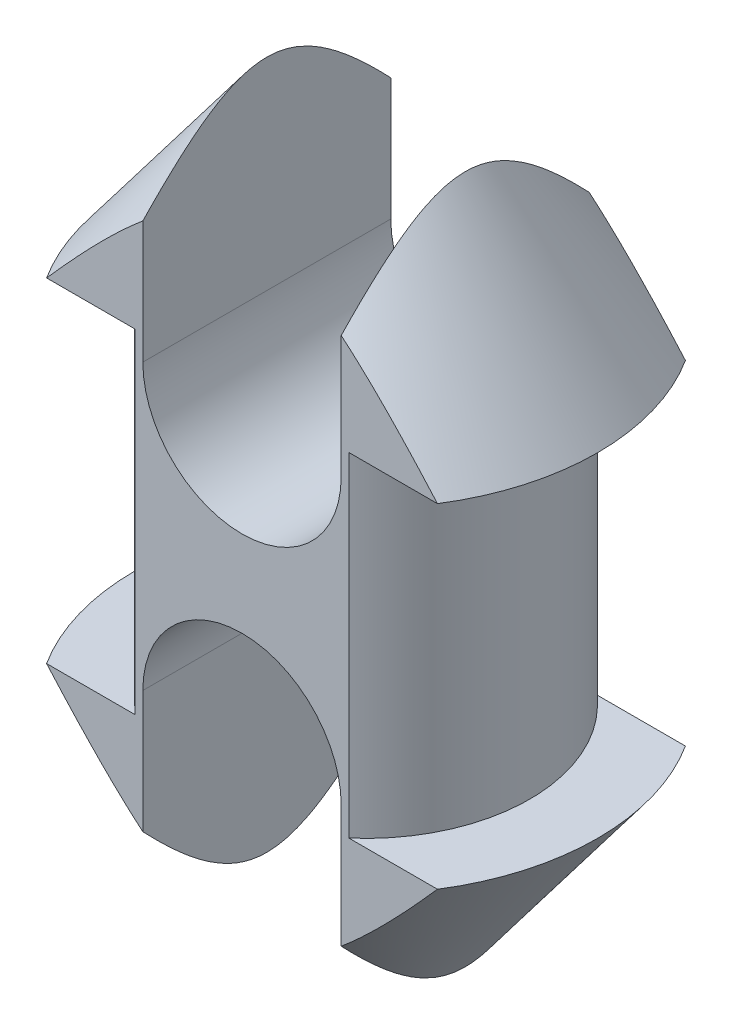
SolidWorks part; units mm, degrees
ref_plane "Plano frontal" through (0, 0, 0) normal (0, 0, 1) x (1, 0, 0)
ref_plane "Plano superior" through (0, 0, 0) normal (0, 1, 0) x (1, 0, 0)
ref_plane "Plano direito" through (0, 0, 0) normal (1, 0, 0) x (0, 0, -1)
sketch "Esboço1" plane through (0, 0, 0) normal (0, 0, 1) x (1, 0, 0)
  line L0 (0, -10.1) -> (0, 10.1) construction
  line L1 (-14, -10.1) -> (-14, 10.1)
  line L2 (14, -10.1) -> (14, 10.1)
  line L3 (14, 10.1) -> (9.9, 10.1)
  line L4 (9.9, 10.1) -> (9.9, -10.1)
  line L5 (9.9, -10.1) -> (14, -10.1)
  line L6 (0, 24.1) -> (0, -24.1)
  line L7 (0, -24.1) -> (0, 85.7647) construction
  line L8 (14, 10.1) -> (4, 23.5164)
  line L9 (14, -10.1) -> (4, -23.5164)
  arc A0 (-14, -10.1) -> (14, -10.1) centre (0, -10.1) ccw
  arc A1 (14, 10.1) -> (-14, 10.1) centre (0, 10.1) ccw
  point P2 (0, 0)
  dimension "D1" = 14
  dimension "D2" = 19.8
  dimension "D3" = 20.2
  dimension "D4" = 4
  dimension "D5" = 4
revolve "Revolução1" add sketch "Esboço1" angle 360 about L7
sketch "Esboço2" plane through (0, 0, 0) normal (0, 1, 0) x (1, 0, 0)
  line L1 (-14, -7.5) -> (14, -7.5)
  line L2 (-14, -7.5) -> (-14, 7.5)
  line L3 (-14, 7.5) -> (14, 7.5)
  line L4 (14, -7.5) -> (14, 7.5)
  line L5 (-14, -7.5) -> (14, 7.5) construction
  line L6 (-14, 7.5) -> (14, -7.5) construction
  circle A0 centre (0, 0) radius 14 construction
  point P0 (0, 0)
  dimension "D1" = 15
extrude "Corte-extrusão1" cut sketch "Esboço2" against normal through all both and the other way through all flip side to cut
sketch "Esboço3" plane through (0, 0, -7.5) normal (0, 0, -1) x (-1, 0, 0)
  line L0 (0, 24.1) -> (0, 8.6) construction
  line L1 (6, 24.1) -> (6, 8.6)
  line L2 (-6, 24.1) -> (-6, 8.6)
  line L3 (0, -24.1) -> (0, -8.6) construction
  line L4 (-6, -24.1) -> (-6, -8.6)
  line L5 (6, -24.1) -> (6, -8.6)
  arc A0 (4, 23.5164) -> (-4, 23.5164) centre (0, 10.1) ccw construction
  arc A1 (6, 24.1) -> (-6, 24.1) centre (0, 24.1) ccw
  arc A2 (-6, 8.6) -> (6, 8.6) centre (0, 8.6) ccw
  arc A3 (-4, -23.5164) -> (4, -23.5164) centre (0, -10.1) ccw construction
  arc A4 (-6, -24.1) -> (6, -24.1) centre (0, -24.1) ccw
  arc A5 (6, -8.6) -> (-6, -8.6) centre (0, -8.6) ccw
  point P6 (0, 16.35)
  point P11 (0, -16.35)
  dimension "D3" = 6
  dimension "D4" = 6
  dimension "D1" = 15.5
  dimension "D2" = 15.5
extrude "Corte-extrusão2" cut sketch "Esboço3" against normal through all
